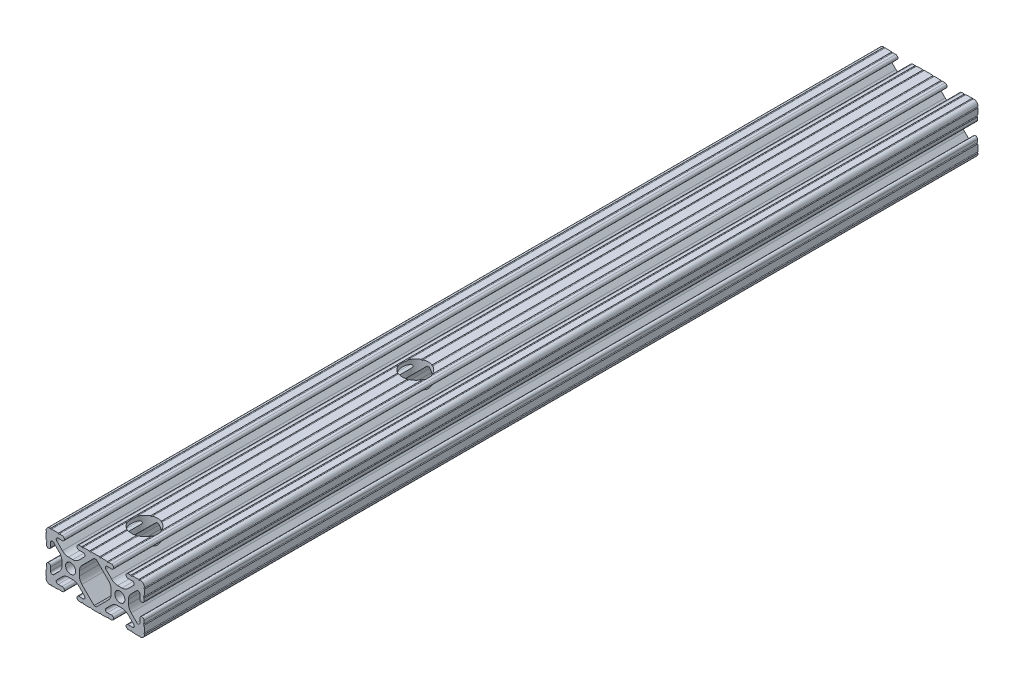
SolidWorks part; units mm, degrees
ref_plane "Front Plane" through (0, 0, 0) normal (0, 0, 1) x (1, 0, 0)
ref_plane "Top Plane" through (0, 0, 0) normal (0, 1, 0) x (1, 0, 0)
ref_plane "Right Plane" through (0, 0, 0) normal (1, 0, 0) x (0, 0, -1)
sketch "Sketch1" plane through (0, 0, 0) normal (0, 0, 1) x (1, 0, 0)
  line L0 (0, 12.7) -> (-12.7814, 12.7) construction
  line L1 (-4.5085, 0) -> (-4.5085, 2.9459)
  line L2 (-6.0437, 12.5461) -> (-10.0976, 12.6876) construction
  line L3 (-11.5616, 12.4229) -> (-4.3159, 12.1699) construction
  line L4 (-6.4364, 10.3486) -> (-6.3592, 12.5571) construction
  line L6 (-2.9459, 4.5085) -> (0, 4.5085)
  line L7 (0, 0) -> (0, 12.7) construction
  line L8 (0, 0) -> (-12.7814, 0) construction
  line L9 (0.7813, 0.7813) -> (-0.7813, -0.7813) construction
  line L10 (-2.9459, 4.5085) -> (-7.1484, 8.711)
  line L11 (-4.5085, 2.9459) -> (-8.711, 7.1484)
  line L13 (0, 0) -> (-12.7814, 12.7814) construction
  line L14 (-10.4131, 12.6987) -> (-4.3048, 12.4853)
  line L15 (-4.3048, 12.4853) -> (-4.382, 10.2769) construction
  line L16 (-4.382, 10.2769) -> (-6.4364, 10.3486)
  line L17 (-12.6987, 10.4131) -> (-12.4853, 4.3048)
  line L18 (-10.2769, 4.382) -> (-10.3486, 6.4364)
  circle A0 centre (0, 0) radius 2.6035
  arc A1 (-4.382, 10.2769) -> (-4.3048, 12.4853) centre (-4.3434, 11.3811) ccw
  arc A2 (-7.1484, 8.711) -> (-6.4364, 10.3486) centre (-6.4698, 9.3896) cw
  arc A3 (-8.711, 7.1484) -> (-10.3486, 6.4364) centre (-9.3896, 6.4698) ccw
  arc A4 (-10.2769, 4.382) -> (-12.4853, 4.3048) centre (-11.3811, 4.3434) cw
  arc A5 (-10.4131, 12.6987) -> (-12.6987, 10.4131) centre (-10.4902, 10.4902) ccw
  arc A6 (-10.4131, 12.6987) -> (-9.7821, 12.6766) centre (-10.0976, 12.6876) ccw
  arc A7 (-6.3592, 12.5571) -> (-5.7282, 12.5351) centre (-6.0437, 12.5461) ccw
  arc A8 (-12.5571, 6.3592) -> (-12.5351, 5.7282) centre (-12.5461, 6.0437) cw
  arc A9 (-12.6987, 10.4131) -> (-12.6766, 9.7821) centre (-12.6876, 10.0976) cw
  dimension "D1" = 5.207
  dimension "D5" = 14.859
  dimension "D9" = 2
  dimension "D2" = 25.4
  dimension "D12" = 0.6314
  dimension "D10" = 2.2098
  dimension "D3" = 9.017
  dimension "D4" = 9.017
  dimension "D6" = 25.4
  dimension "D7" = 6.477
  dimension "D8" = 2.2098
  dimension "D11" = 12.7
sketch "Sketch3" plane through (0, 0, 0) normal (0, 0, 1) x (1, 0, 0)
  line L0 (-2.9459, 4.5085) -> (0, 4.5085) construction
  line L1 (-2.9459, 4.5085) -> (-7.1484, 8.711) construction
  line L2 (-4.382, 10.2769) -> (-6.4364, 10.3486) construction
  line L3 (-10.4131, 12.6987) -> (-4.3048, 12.4853) construction
  line L4 (-4.5085, 0) -> (-4.5085, 2.9459) construction
  line L5 (-4.5085, 2.9459) -> (-8.711, 7.1484) construction
  line L6 (-10.2769, 4.382) -> (-10.3486, 6.4364) construction
  line L7 (-12.6987, 10.4131) -> (-12.4853, 4.3048) construction
  line L8 (-1.1153, 4.5085) -> (1.1153, 4.5085)
  line L9 (-4.2404, 5.803) -> (-7.1484, 8.711)
  line L10 (-4.382, 10.2769) -> (-6.4364, 10.3486)
  line L11 (-9.7821, 12.6766) -> (-6.3592, 12.5571)
  line L12 (-4.5085, -1.1153) -> (-4.5085, 1.1153)
  line L13 (-5.803, 4.2404) -> (-8.711, 7.1484)
  line L14 (-10.2769, 4.382) -> (-10.3486, 6.4364)
  line L15 (-12.6766, 9.7821) -> (-12.5571, 6.3592)
  line L16 (-5.7282, 12.5351) -> (-4.3048, 12.4853)
  line L17 (-12.5351, 5.7282) -> (-12.4853, 4.3048)
  line L18 (0, 0) -> (0, 12.7) construction
  line L19 (0, 0) -> (-12.7814, 0) construction
  line L20 (0, 0) -> (12.7, 0) construction
  line L21 (5.7282, 12.5351) -> (4.3048, 12.4853)
  line L22 (12.7, 10.5674) -> (12.7, 12.6987) construction
  line L23 (10.4131, 12.6987) -> (14.9869, 12.6987)
  line L24 (5.803, 4.2404) -> (12.1093, 10.5467)
  line L25 (4.5085, -1.1153) -> (4.5085, 1.1153)
  line L26 (9.7821, 12.6766) -> (6.3592, 12.5571)
  line L27 (4.382, 10.2769) -> (6.4364, 10.3486)
  line L28 (4.2404, 5.803) -> (7.1484, 8.711)
  line L29 (4.2404, -5.803) -> (7.1484, -8.711)
  line L30 (4.382, -10.2769) -> (6.4364, -10.3486)
  line L31 (9.7821, -12.6766) -> (6.3592, -12.5571)
  line L32 (5.803, -4.2404) -> (12.1093, -10.5467)
  line L33 (12.1093, 10.5467) -> (12.7, 10.5674)
  line L34 (10.4131, -12.6987) -> (14.9869, -12.6987)
  line L35 (5.7282, -12.5351) -> (4.3048, -12.4853)
  line L36 (12.7, -10.5674) -> (12.7, -12.6987) construction
  line L37 (-12.5351, -5.7282) -> (-12.4853, -4.3048)
  line L38 (-5.7282, -12.5351) -> (-4.3048, -12.4853)
  line L39 (-12.6766, -9.7821) -> (-12.5571, -6.3592)
  line L40 (-10.2769, -4.382) -> (-10.3486, -6.4364)
  line L41 (-5.803, -4.2404) -> (-8.711, -7.1484)
  line L42 (-9.7821, -12.6766) -> (-6.3592, -12.5571)
  line L43 (-4.382, -10.2769) -> (-6.4364, -10.3486)
  line L44 (-4.2404, -5.803) -> (-7.1484, -8.711)
  line L45 (-1.1153, -4.5085) -> (1.1153, -4.5085)
  line L46 (12.1093, -10.5467) -> (12.7, -10.5674)
  line L47 (13.2907, -10.5467) -> (12.7, -10.5674)
  line L48 (26.5153, -4.5085) -> (24.2847, -4.5085)
  line L49 (29.6404, -5.803) -> (32.5484, -8.711)
  line L50 (29.782, -10.2769) -> (31.8364, -10.3486)
  line L51 (35.1821, -12.6766) -> (31.7592, -12.5571)
  line L52 (31.203, -4.2404) -> (34.111, -7.1484)
  line L53 (35.6769, -4.382) -> (35.7486, -6.4364)
  line L54 (38.0766, -9.7821) -> (37.9571, -6.3592)
  line L55 (31.1282, -12.5351) -> (29.7048, -12.4853)
  line L56 (37.9351, -5.7282) -> (37.8853, -4.3048)
  line L57 (19.6718, -12.5351) -> (21.0952, -12.4853)
  line L58 (13.2907, 10.5467) -> (12.7, 10.5674)
  line L59 (19.597, -4.2404) -> (13.2907, -10.5467)
  line L60 (15.6179, -12.6766) -> (19.0408, -12.5571)
  line L61 (21.018, -10.2769) -> (18.9636, -10.3486)
  line L62 (21.1596, -5.803) -> (18.2516, -8.711)
  line L63 (21.1596, 5.803) -> (18.2516, 8.711)
  line L64 (21.018, 10.2769) -> (18.9636, 10.3486)
  line L65 (15.6179, 12.6766) -> (19.0408, 12.5571)
  line L66 (20.8915, -1.1153) -> (20.8915, 1.1153)
  line L67 (19.597, 4.2404) -> (13.2907, 10.5467)
  line L68 (19.6718, 12.5351) -> (21.0952, 12.4853)
  line L69 (37.9351, 5.7282) -> (37.8853, 4.3048)
  line L70 (31.1282, 12.5351) -> (29.7048, 12.4853)
  line L71 (38.0766, 9.7821) -> (37.9571, 6.3592)
  line L72 (35.6769, 4.382) -> (35.7486, 6.4364)
  line L73 (31.203, 4.2404) -> (34.111, 7.1484)
  line L74 (29.9085, -1.1153) -> (29.9085, 1.1153)
  line L75 (35.1821, 12.6766) -> (31.7592, 12.5571)
  line L76 (29.782, 10.2769) -> (31.8364, 10.3486)
  line L77 (29.6404, 5.803) -> (32.5484, 8.711)
  line L78 (26.5153, 4.5085) -> (24.2847, 4.5085)
  arc A0 (-10.4131, 12.6987) -> (-9.7821, 12.6766) centre (-10.0976, 12.6876) ccw construction
  arc A1 (-6.4364, 10.3486) -> (-7.1484, 8.711) centre (-6.4698, 9.3896) ccw construction
  arc A2 (-4.382, 10.2769) -> (-4.3048, 12.4853) centre (-4.3434, 11.3811) ccw construction
  arc A3 (-8.711, 7.1484) -> (-10.3486, 6.4364) centre (-9.3896, 6.4698) ccw construction
  arc A4 (-12.4853, 4.3048) -> (-10.2769, 4.382) centre (-11.3811, 4.3434) ccw construction
  arc A5 (-6.3592, 12.5571) -> (-5.7282, 12.5351) centre (-6.0437, 12.5461) ccw construction
  arc A6 (-10.4131, 12.6987) -> (-12.6987, 10.4131) centre (-10.4902, 10.4902) ccw construction
  arc A7 (-12.6766, 9.7821) -> (-12.6987, 10.4131) centre (-12.6876, 10.0976) ccw construction
  arc A8 (-12.5351, 5.7282) -> (-12.5571, 6.3592) centre (-12.5461, 6.0437) ccw construction
  arc A9 (-10.4131, 12.6987) -> (-9.7821, 12.6766) centre (-10.0976, 12.6876) ccw
  arc A10 (-6.4364, 10.3486) -> (-7.1484, 8.711) centre (-6.4698, 9.3896) ccw
  arc A11 (-4.382, 10.2769) -> (-4.3048, 12.4853) centre (-4.3434, 11.3811) ccw
  arc A12 (-8.711, 7.1484) -> (-10.3486, 6.4364) centre (-9.3896, 6.4698) ccw
  arc A13 (-12.4853, 4.3048) -> (-10.2769, 4.382) centre (-11.3811, 4.3434) ccw
  arc A14 (-6.3592, 12.5571) -> (-5.7282, 12.5351) centre (-6.0437, 12.5461) ccw
  arc A15 (-10.4131, 12.6987) -> (-12.6987, 10.4131) centre (-10.4902, 10.4902) ccw
  arc A16 (-12.6766, 9.7821) -> (-12.6987, 10.4131) centre (-12.6876, 10.0976) ccw
  arc A17 (-12.5351, 5.7282) -> (-12.5571, 6.3592) centre (-12.5461, 6.0437) ccw
  arc A18 (-1.1153, 4.5085) -> (-4.2404, 5.803) centre (-1.1153, 8.9281) cw
  arc A19 (4.5085, 1.1153) -> (5.803, 4.2404) centre (8.9281, 1.1153) cw
  arc A20 (1.1153, 4.5085) -> (4.2404, 5.803) centre (1.1153, 8.9281) ccw
  arc A21 (-4.5085, 1.1153) -> (-5.803, 4.2404) centre (-8.9281, 1.1153) ccw
  circle A22 centre (25.4, 0) radius 2.6035
  arc A23 (35.8131, -12.6987) -> (35.1821, -12.6766) centre (35.4976, -12.6876) ccw
  arc A24 (31.8364, -10.3486) -> (32.5484, -8.711) centre (31.8698, -9.3896) ccw
  arc A25 (6.3592, 12.5571) -> (5.7282, 12.5351) centre (6.0437, 12.5461) cw
  arc A26 (29.782, -10.2769) -> (29.7048, -12.4853) centre (29.7434, -11.3811) ccw
  arc A27 (34.111, -7.1484) -> (35.7486, -6.4364) centre (34.7896, -6.4698) ccw
  arc A28 (4.382, 10.2769) -> (4.3048, 12.4853) centre (4.3434, 11.3811) cw
  arc A29 (6.4364, 10.3486) -> (7.1484, 8.711) centre (6.4698, 9.3896) cw
  arc A30 (10.4131, 12.6987) -> (9.7821, 12.6766) centre (10.0976, 12.6876) cw
  arc A31 (10.4131, -12.6987) -> (9.7821, -12.6766) centre (10.0976, -12.6876) ccw
  arc A32 (6.4364, -10.3486) -> (7.1484, -8.711) centre (6.4698, -9.3896) ccw
  arc A33 (4.382, -10.2769) -> (4.3048, -12.4853) centre (4.3434, -11.3811) ccw
  arc A34 (37.8853, -4.3048) -> (35.6769, -4.382) centre (36.7811, -4.3434) ccw
  arc A35 (31.7592, -12.5571) -> (31.1282, -12.5351) centre (31.4437, -12.5461) ccw
  arc A36 (6.3592, -12.5571) -> (5.7282, -12.5351) centre (6.0437, -12.5461) ccw
  arc A37 (35.8131, -12.6987) -> (38.0987, -10.4131) centre (35.8902, -10.4902) ccw
  arc A38 (38.0766, -9.7821) -> (38.0987, -10.4131) centre (38.0876, -10.0976) ccw
  arc A39 (37.9351, -5.7282) -> (37.9571, -6.3592) centre (37.9461, -6.0437) ccw
  arc A40 (-4.5085, -1.1153) -> (-5.803, -4.2404) centre (-8.9281, -1.1153) cw
  arc A41 (1.1153, -4.5085) -> (4.2404, -5.803) centre (1.1153, -8.9281) cw
  arc A42 (4.5085, -1.1153) -> (5.803, -4.2404) centre (8.9281, -1.1153) ccw
  arc A43 (-1.1153, -4.5085) -> (-4.2404, -5.803) centre (-1.1153, -8.9281) ccw
  arc A44 (-12.5351, -5.7282) -> (-12.5571, -6.3592) centre (-12.5461, -6.0437) cw
  arc A45 (-12.6766, -9.7821) -> (-12.6987, -10.4131) centre (-12.6876, -10.0976) cw
  arc A46 (-10.4131, -12.6987) -> (-12.6987, -10.4131) centre (-10.4902, -10.4902) cw
  arc A47 (-6.3592, -12.5571) -> (-5.7282, -12.5351) centre (-6.0437, -12.5461) cw
  arc A48 (-12.4853, -4.3048) -> (-10.2769, -4.382) centre (-11.3811, -4.3434) cw
  arc A49 (-8.711, -7.1484) -> (-10.3486, -6.4364) centre (-9.3896, -6.4698) cw
  arc A50 (-4.382, -10.2769) -> (-4.3048, -12.4853) centre (-4.3434, -11.3811) cw
  arc A51 (-6.4364, -10.3486) -> (-7.1484, -8.711) centre (-6.4698, -9.3896) cw
  arc A52 (-10.4131, -12.6987) -> (-9.7821, -12.6766) centre (-10.0976, -12.6876) cw
  circle A53 centre (0, 0) radius 2.6035 construction
  circle A54 centre (0, 0) radius 2.6035
  arc A55 (26.5153, -4.5085) -> (29.6404, -5.803) centre (26.5153, -8.9281) cw
  arc A56 (20.8915, -1.1153) -> (19.597, -4.2404) centre (16.4719, -1.1153) cw
  arc A57 (24.2847, -4.5085) -> (21.1596, -5.803) centre (24.2847, -8.9281) ccw
  arc A58 (29.9085, -1.1153) -> (31.203, -4.2404) centre (34.3281, -1.1153) ccw
  arc A59 (19.0408, -12.5571) -> (19.6718, -12.5351) centre (19.3563, -12.5461) cw
  arc A60 (21.018, -10.2769) -> (21.0952, -12.4853) centre (21.0566, -11.3811) cw
  arc A61 (18.9636, -10.3486) -> (18.2516, -8.711) centre (18.9302, -9.3896) cw
  arc A62 (14.9869, -12.6987) -> (15.6179, -12.6766) centre (15.3024, -12.6876) cw
  arc A63 (14.9869, 12.6987) -> (15.6179, 12.6766) centre (15.3024, 12.6876) ccw
  arc A64 (18.9636, 10.3486) -> (18.2516, 8.711) centre (18.9302, 9.3896) ccw
  arc A65 (21.018, 10.2769) -> (21.0952, 12.4853) centre (21.0566, 11.3811) ccw
  arc A66 (19.0408, 12.5571) -> (19.6718, 12.5351) centre (19.3563, 12.5461) ccw
  arc A67 (29.9085, 1.1153) -> (31.203, 4.2404) centre (34.3281, 1.1153) cw
  arc A68 (24.2847, 4.5085) -> (21.1596, 5.803) centre (24.2847, 8.9281) cw
  arc A69 (20.8915, 1.1153) -> (19.597, 4.2404) centre (16.4719, 1.1153) ccw
  arc A70 (26.5153, 4.5085) -> (29.6404, 5.803) centre (26.5153, 8.9281) ccw
  arc A71 (37.9351, 5.7282) -> (37.9571, 6.3592) centre (37.9461, 6.0437) cw
  arc A72 (38.0766, 9.7821) -> (38.0987, 10.4131) centre (38.0876, 10.0976) cw
  arc A73 (35.8131, 12.6987) -> (38.0987, 10.4131) centre (35.8902, 10.4902) cw
  arc A74 (31.7592, 12.5571) -> (31.1282, 12.5351) centre (31.4437, 12.5461) cw
  arc A75 (37.8853, 4.3048) -> (35.6769, 4.382) centre (36.7811, 4.3434) cw
  arc A76 (34.111, 7.1484) -> (35.7486, 6.4364) centre (34.7896, 6.4698) cw
  arc A77 (29.782, 10.2769) -> (29.7048, 12.4853) centre (29.7434, 11.3811) cw
  arc A78 (31.8364, 10.3486) -> (32.5484, 8.711) centre (31.8698, 9.3896) cw
  arc A79 (35.8131, 12.6987) -> (35.1821, 12.6766) centre (35.4976, 12.6876) cw
  point P135 (4.5085, 0)
  point P218 (20.8915, 0)
  dimension "D2" = 4.4196
  dimension "D1" = 12.7
extrude "Extrude1" add sketch "Sketch3" along normal blind 430
sketch "Sketch4" plane through (0, 12.6987, 0) normal (0, 1, 0) x (1, 0, 0)
  line L0 (12.7, -430) -> (12.7, -404.6)
  line L1 (14.9869, -430) -> (10.4131, -430) construction
  line L2 (12.7, -404.6) -> (12.7, -264.9)
  circle A0 centre (12.7, -404.6) radius 6.75
  circle A1 centre (12.7, -264.9) radius 6.75
  dimension "D2" = 13.5
  dimension "D4" = 13.5
  dimension "D1" = 25.4
  dimension "D3" = 139.7
extrude "Cut-Extrude2" cut sketch "Sketch4" against normal through all
equation "\"D10@Sketch1\" = \"D8@Sketch1\""
equation "\"D11@Sketch1\" = \"D6@Sketch1\"/2"
equation "\"D12@Sketch1\" = \"D8@Sketch1\"/3.5"
equation "\"D2@Sketch3\" = \"D8@Sketch1\"*2"
